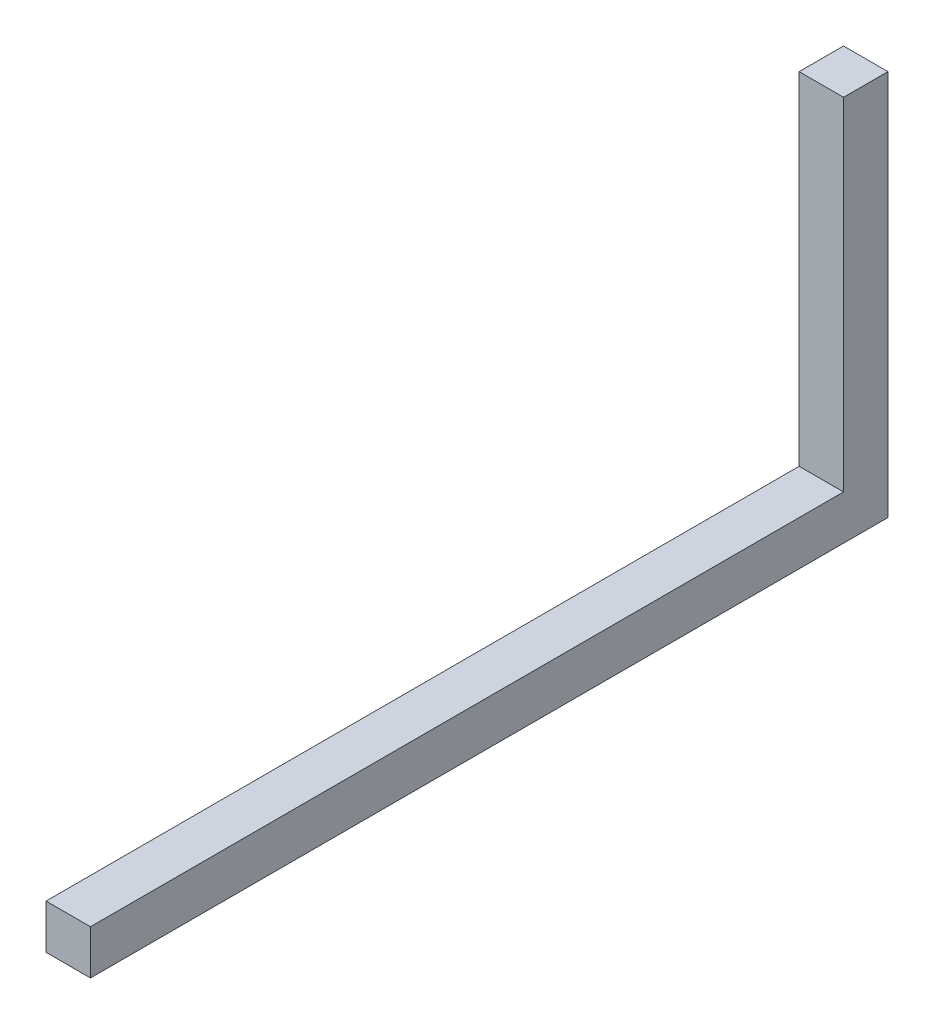
SolidWorks part; units mm, degrees
ref_plane "Front Plane" through (0, 0, 0) normal (0, 0, 1) x (1, 0, 0)
ref_plane "Top Plane" through (0, 0, 0) normal (0, 1, 0) x (1, 0, 0)
ref_plane "Right Plane" through (0, 0, 0) normal (1, 0, 0) x (0, 0, -1)
sketch "Sketch1" plane through (0, 0, 0) normal (0, 0, 1) x (1, 0, 0)
  line L1 (5.75, 5.75) -> (-5.75, 5.75)
  line L2 (5.75, 5.75) -> (5.75, -5.75)
  line L3 (5.75, -5.75) -> (-5.75, -5.75)
  line L4 (-5.75, 5.75) -> (-5.75, -5.75)
  line L5 (5.75, 5.75) -> (-5.75, -5.75) construction
  line L6 (5.75, -5.75) -> (-5.75, 5.75) construction
  point P0 (0, 0)
  dimension "D1" = 11.5
  dimension "D2" = 11.5
extrude "Boss-Extrude1" add sketch "Sketch1" along normal blind 195
sketch "Sketch2" plane through (0, 0, 0) normal (0, 1, 0) x (1, 0, 0)
  line L1 (5.75, 0) -> (-5.75, 0)
  line L2 (5.75, 0) -> (5.75, 11.5)
  line L3 (5.75, 11.5) -> (-5.75, 11.5)
  line L4 (-5.75, 0) -> (-5.75, 11.5)
  dimension "D1" = 11.5
  dimension "D2" = 11.5
extrude "Boss-Extrude2" add sketch "Sketch2" along normal blind 100 from surface at -5.75 starting at face at (0, -5.75, 97.5)
